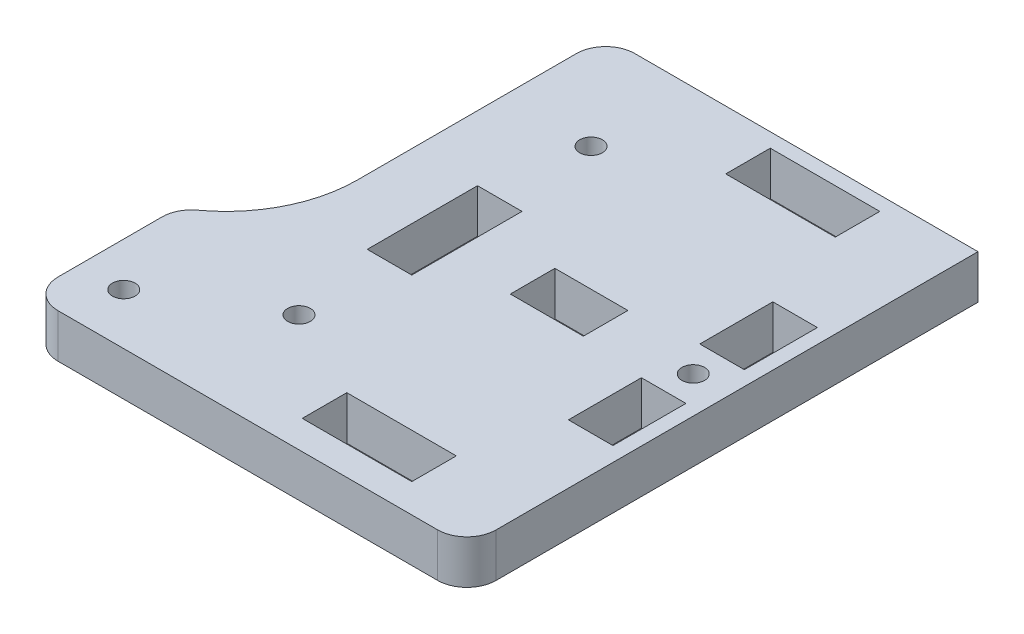
SolidWorks part; units mm, degrees
ref_plane "Спереди" through (0, 0, 0) normal (0, 0, 1) x (1, 0, 0)
ref_plane "Сверху" through (0, 0, 0) normal (0, 1, 0) x (1, 0, 0)
ref_plane "Справа" through (0, 0, 0) normal (1, 0, 0) x (0, 0, -1)
sketch "Эскиз1" plane through (0, 0, 0) normal (0, 1, 0) x (1, 0, 0)
  line L0 (12.1477, 6.1861) -> (18.2477, 6.1861)
  line L1 (18.2477, 6.1861) -> (18.2477, 16.1861)
  line L2 (18.2477, 16.1861) -> (12.1477, 16.1861)
  line L3 (12.1477, 16.1861) -> (12.1477, 6.1861)
  line L4 (-21.8523, -5.3639) -> (-15.7523, -5.3639)
  line L5 (-15.7523, -5.3639) -> (-15.7523, 9.7361)
  line L6 (-15.7523, 9.7361) -> (-21.8523, 9.7361)
  line L7 (-21.8523, 9.7361) -> (-21.8523, -5.3639)
  line L8 (3.2477, 5.2361) -> (-6.7523, 5.2361)
  line L9 (-6.7523, 5.2361) -> (-6.7523, -0.8639)
  line L10 (-6.7523, -0.8639) -> (3.2477, -0.8639)
  line L11 (3.2477, -0.8639) -> (3.2477, 5.2361)
  line L12 (18.2477, -11.8139) -> (18.2477, -1.8139)
  line L13 (18.2477, -1.8139) -> (12.1477, -1.8139)
  line L14 (12.1477, -1.8139) -> (12.1477, -11.8139)
  line L15 (12.1477, -11.8139) -> (18.2477, -11.8139)
  line L16 (8.7477, 34.2361) -> (-6.2523, 34.2361)
  line L17 (-6.2523, 34.2361) -> (-6.2523, 28.1361)
  line L18 (-6.2523, 28.1361) -> (8.7477, 28.1361)
  line L19 (8.7477, 28.1361) -> (8.7477, 34.2361)
  line L20 (-6.2523, -29.8639) -> (8.7477, -29.8639)
  line L21 (8.7477, -29.8639) -> (8.7477, -23.7639)
  line L22 (8.7477, -23.7639) -> (-6.2523, -23.7639)
  line L23 (-6.2523, -23.7639) -> (-6.2523, -29.8639)
  line L24 (-35.7523, -33.8139) -> (16.2477, -33.8139)
  line L25 (-39.7523, -15.5621) -> (-39.7523, -29.8139)
  line L26 (-30.7523, 32.1861) -> (-30.7523, 2.1861)
  line L27 (20.2477, 36.1861) -> (-26.7523, 36.1861)
  line L28 (20.2477, -29.8139) -> (20.2477, 36.1861)
  arc A0 (-26.7523, 36.1861) -> (-30.7523, 32.1861) centre (-26.7523, 32.1861) ccw
  arc A1 (16.2477, -33.8139) -> (20.2477, -29.8139) centre (16.2477, -29.8139) ccw
  arc A2 (-39.7523, -29.8139) -> (-35.7523, -33.8139) centre (-35.7523, -29.8139) ccw
  arc A3 (-38.116, -12.3352) -> (-39.7523, -15.5621) centre (-35.7523, -15.5621) ccw
  circle A4 centre (15.2477, 2.1861) radius 1.55
  circle A5 centre (-18.7523, -17.8139) radius 1.55
  circle A6 centre (-33.7523, -26.8139) radius 1.55
  circle A7 centre (-18.7523, 22.1861) radius 1.55
  arc A8 (-38.116, -12.3352) -> (-30.7523, 2.1861) centre (-48.7523, 2.1861) ccw
extrude "Бобышка-Вытянуть1" add sketch "Эскиз1" along normal blind 6
